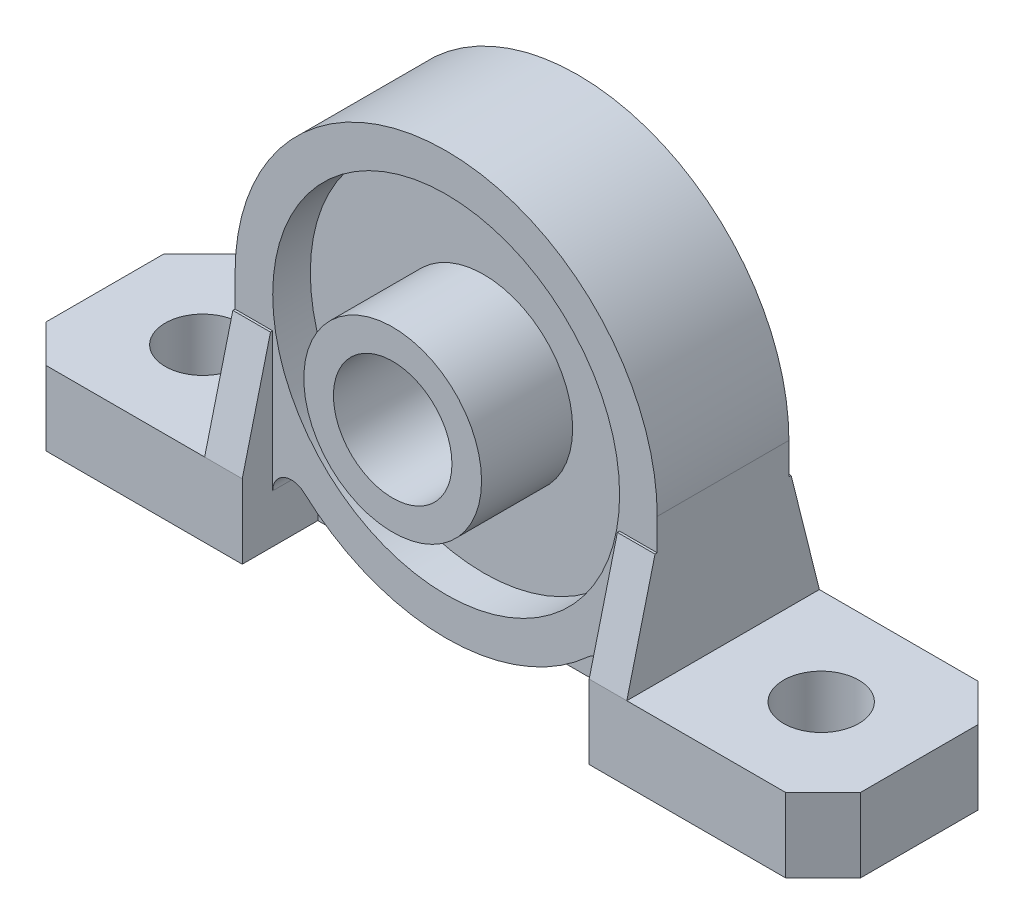
SolidWorks part; units mm, degrees
ref_plane "Front Plane" through (0, 0, 0) normal (0, 0, 1) x (1, 0, 0)
ref_plane "Top Plane" through (0, 0, 0) normal (0, 1, 0) x (1, 0, 0)
ref_plane "Right Plane" through (0, 0, 0) normal (1, 0, 0) x (0, 0, -1)
sketch "Sketch1" plane through (0, 0, 0) normal (0, 1, 0) x (1, 0, 0)
  line L1 (-27.5, -6.5) -> (27.5, -6.5)
  line L2 (-27.5, -6.5) -> (-27.5, 6.5)
  line L3 (-27.5, 6.5) -> (27.5, 6.5)
  line L4 (27.5, -6.5) -> (27.5, 6.5)
  line L5 (-27.5, -6.5) -> (27.5, 6.5) construction
  line L6 (-27.5, 6.5) -> (27.5, -6.5) construction
  point P0 (0, 0)
  dimension "D1" = 55
  dimension "D2" = 13
extrude "Boss-Extrude1" add sketch "Sketch1" along normal blind 29
sketch "Sketch2" plane through (0, 0, 6.5) normal (0, 0, 1) x (1, 0, 0)
  line L0 (27.5, 5) -> (14.25, 5)
  line L1 (27.5, 29) -> (27.5, 0) construction
  line L2 (14.25, 5) -> (14.25, 14.75)
  line L3 (14.25, 14.75) -> (-14.25, 14.75)
  line L4 (-14.25, 14.75) -> (-14.25, 5)
  line L5 (-14.25, 5) -> (-27.5, 5)
  line L6 (-27.5, 29) -> (-27.5, 0) construction
  line L7 (-27.5, 0) -> (27.5, 0) construction
  line L8 (-27.5, 5) -> (-27.5, 0)
  line L9 (-27.5, 0) -> (27.5, 0)
  line L10 (27.5, 0) -> (27.5, 5)
  line L11 (-27.5, 29) -> (27.5, 29) construction
  line L12 (-27.5, 5) -> (-27.5, 29)
  line L13 (-27.5, 29) -> (27.5, 29)
  line L14 (27.5, 29) -> (27.5, 5)
  arc A0 (-14.25, 14.75) -> (14.25, 14.75) centre (0, 14.75) cw
  dimension "D3" = 14.25
  dimension "D1" = 5
  dimension "D2" = 5
extrude "Cut-Extrude1" cut sketch "Sketch2" against normal through all contours L4 A0 L13 L5 M6 | A0 L2 L0 M5 M4
sketch "Sketch3" plane through (0, 5, 0) normal (0, 1, 0) x (1, 0, 0)
  line L1 (-14.25, -4.445) -> (14.25, -4.445)
  line L2 (-14.25, -4.445) -> (-14.25, 4.445)
  line L3 (-14.25, 4.445) -> (14.25, 4.445)
  line L4 (14.25, -4.445) -> (14.25, 4.445)
  line L5 (-14.25, -4.445) -> (14.25, 4.445) construction
  line L6 (-14.25, 4.445) -> (14.25, -4.445) construction
  line L7 (14.25, 6.5) -> (14.25, -6.5) construction
  point P0 (0, 0)
  dimension "D1" = 8.89
extrude "Cut-Extrude2" cut sketch "Sketch3" along normal through all flip side to cut
sketch "Sketch5" plane through (0, 0, 0) normal (0, 0, 1) x (1, 0, 0)
  line L0 (14.25, 5) -> (14.25, 14.75) construction
  line L1 (14.25, 12.62) -> (11.71, 12.62)
  line L2 (14.25, 12.62) -> (14.25, 5)
  line L3 (14.25, 5) -> (11.71, 5)
  line L4 (11.71, 12.62) -> (11.71, 5)
  line L5 (27.5, 5) -> (-27.5, 5) construction
  line L6 (-14.25, 14.75) -> (-14.25, 5) construction
  line L7 (-14.25, 12.62) -> (-11.71, 12.62)
  line L8 (-14.25, 12.62) -> (-14.25, 5)
  line L9 (-14.25, 5) -> (-11.71, 5)
  line L10 (-11.71, 12.62) -> (-11.71, 5)
  dimension "D1" = 2.54
  dimension "D2" = 7.62
  dimension "D3" = 7.62
  dimension "D4" = 2.54
extrude "Boss-Extrude2" add sketch "Sketch5" along normal through all and the other way through all
chamfer "Chamfer1" distance 1.905 distance2 7.62 2 edges at (12.98, 12.62, 6.5) (-12.98, 12.62, 6.5)
chamfer "Chamfer2" distance 7.62 distance2 1.905 2 edges at (-12.98, 12.62, -6.5) (12.98, 12.62, -6.5)
sketch "Sketch6" plane through (0, 0, 0) normal (0, 0, 1) x (1, 0, 0)
  line L0 (11.71, 3.2662) -> (11.71, 0)
  line L1 (-27.5, 0) -> (27.5, 0) construction
  line L2 (11.71, 0) -> (-11.71, 0)
  line L3 (-11.71, 0) -> (-11.71, 3.2662)
  line L4 (-11.71, 5) -> (-11.71, 12.62) construction
  line L5 (11.71, 12.62) -> (11.71, 5) construction
  arc A1 (14.25, 14.75) -> (-14.25, 14.75) centre (0, 14.75) ccw construction
  arc A2 (9.5857, 4.206) -> (11.71, 3.2662) centre (10.44, 3.2662) cw
  arc A4 (-9.5857, 4.206) -> (9.5857, 4.206) centre (0, 14.75) ccw
  arc A5 (-9.5857, 4.206) -> (-11.71, 3.2662) centre (-10.44, 3.2662) ccw
  point P12 (0, 0.5)
  dimension "D1" = 1.27
extrude "Cut-Extrude3" cut sketch "Sketch6" against normal through all from offset 1.397 offset against normal yes
sketch "Sketch7" plane through (0, 0, 0) normal (0, 0, 1) x (1, 0, 0)
  line L0 (-11.71, 12.62) -> (-11.71, 0)
  line L1 (-11.71, 0) -> (11.71, 0)
  line L2 (11.71, 0) -> (11.71, 12.62)
  line L3 (11.71, 12.62) -> (-11.71, 12.62)
  line L5 (-11.71, 5) -> (-11.71, 12.62) construction
  line L6 (11.71, 12.62) -> (11.71, 5) construction
extrude "Cut-Extrude4" cut sketch "Sketch7" against normal through all from offset 4.445 offset against normal yes
sketch "Sketch8" plane through (0, 0, 0) normal (0, 0, 1) x (1, 0, 0)
  line L0 (-11.71, 0) -> (-27.5, 0) construction
  circle A0 centre (0, 14.5) radius 4
  dimension "D1" = 8
  dimension "D2" = 14.5
extrude "Cut-Extrude5" cut sketch "Sketch8" against normal through all and the other way through all
sketch "Sketch9" plane through (0, 0, -4.445) normal (0, 0, -1) x (-1, 0, 0)
  arc A2 (11.71, 14.75) -> (-11.71, 14.75) centre (0, 14.75) ccw
  circle A3 centre (0, 14.75) radius 11.71
  dimension "D1" = 2.54
extrude "Cut-Extrude6" cut sketch "Sketch9" against normal blind 2.54
mirror "Mirror1" about plane through (0, 0, 0) normal (0, 0, 1) of "Cut-Extrude3", "Cut-Extrude4", "Cut-Extrude6"
chamfer "Chamfer3" distance 2.54 angle 45 4 edges at (-27.5, 2.5, 6.5) (-27.5, 2.5, -6.5) (27.5, 2.5, 6.5) (27.5, 2.5, -6.5)
sketch "Sketch10" plane through (0, 5, 0) normal (0, 1, 0) x (1, 0, 0)
  line L0 (14.25, 0) -> (27.5, 0) construction
  line L1 (14.25, 6.5) -> (14.25, -6.5) construction
  line L2 (27.5, 3.96) -> (27.5, -3.96) construction
  circle A0 centre (20.875, 0) radius 2.54
  dimension "D1" = 5.08
extrude "Cut-Extrude7" cut sketch "Sketch10" against normal through all
mirror "Mirror2" about plane through (0, 0, 0) normal (1, 0, 0) of "Cut-Extrude7"
sketch "Sketch11" plane through (0, 0, 1.905) normal (0, 0, 1) x (1, 0, 0)
  circle A0 centre (0, 14.5) radius 4
  circle A2 centre (0, 14.5) radius 6
  dimension "D1" = 2
extrude "Boss-Extrude3" add sketch "Sketch11" along normal blind 6.15
